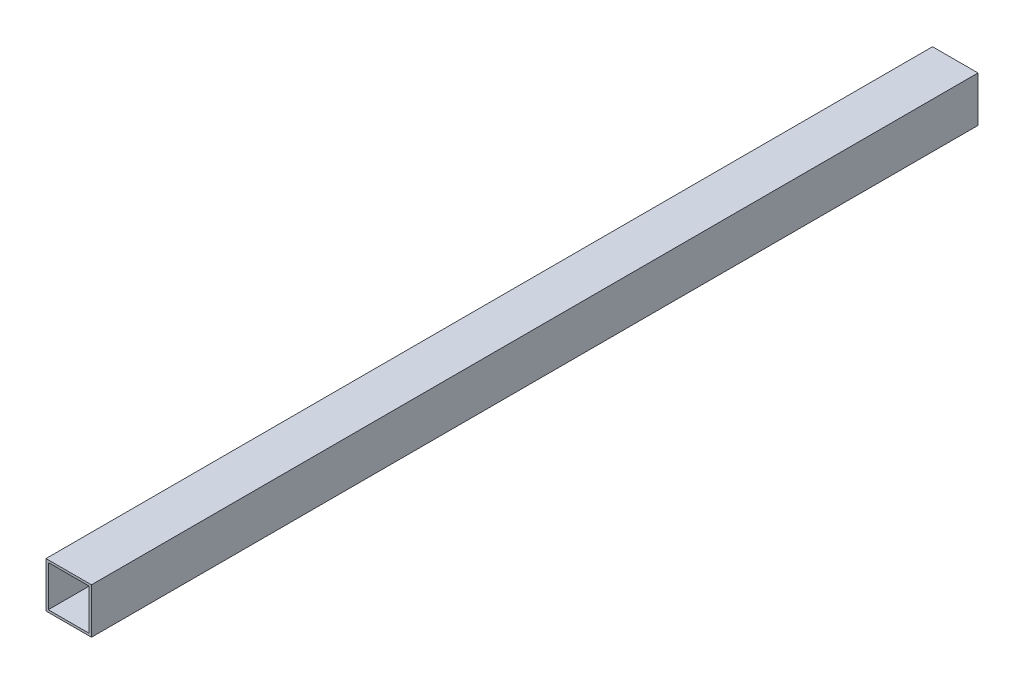
SolidWorks part; units mm, degrees
ref_plane "Front Plane" through (0, 0, 0) normal (0, 0, 1) x (1, 0, 0)
ref_plane "Top Plane" through (0, 0, 0) normal (0, 1, 0) x (1, 0, 0)
ref_plane "Right Plane" through (0, 0, 0) normal (1, 0, 0) x (0, 0, -1)
sketch "Sketch1" plane through (0, 0, 0) normal (0, 0, 1) x (1, 0, 0)
  line L1 (0, 0) -> (20, 0)
  line L2 (0, 0) -> (0, -20)
  line L3 (0, -20) -> (20, -20)
  line L4 (20, 0) -> (20, -20)
  line L5 (1, -19) -> (19, -19)
  line L6 (1, -19) -> (1, -1)
  line L7 (1, -1) -> (19, -1)
  line L8 (19, -19) -> (19, -1)
  line L9 (1, -19) -> (19, -1) construction
  line L10 (1, -1) -> (19, -19) construction
  point P5 (10, -10)
  dimension "D1" = 20
  dimension "D2" = 20
  dimension "D3" = 1
  dimension "D4" = 1
  dimension "D5" = 1
  dimension "D6" = 1
extrude "Boss-Extrude1" add sketch "Sketch1" along normal blind 390
